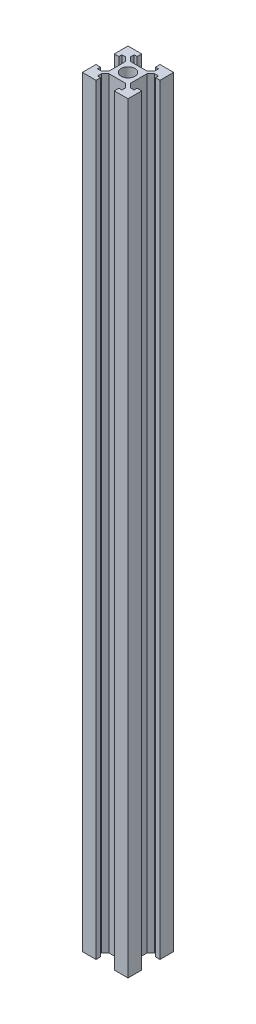
SolidWorks part; units mm, degrees
ref_plane "Front Plane" through (0, 0, 0) normal (0, 0, 1) x (1, 0, 0)
ref_plane "Top Plane" through (0, 0, 0) normal (0, 1, 0) x (1, 0, 0)
ref_plane "Right Plane" through (0, 0, 0) normal (1, 0, 0) x (0, 0, -1)
sketch "Sketch1" plane through (0, 0, 0) normal (0, 1, 0) x (1, 0, 0)
  line L0 (-30, 0) -> (30, 0) construction
  line L3 (-30, 30) -> (-12, 30)
  line L5 (-30, -30) -> (30, 30) construction
  line L6 (-30, 30) -> (30, -30) construction
  line L7 (0, 30) -> (0, -30) construction
  line L8 (-30, 12) -> (-24, 12)
  line L13 (-24, -24) -> (24, 24) construction
  line L14 (-24, 24) -> (24, -24) construction
  line L15 (-14, 24) -> (-14, 16) construction
  line L16 (-24, 16) -> (-19, 16)
  line L17 (-19, 16) -> (-14, 11)
  line L18 (-30, 12) -> (-30, 30)
  line L19 (-14, 11) -> (-14, -11)
  line L20 (-24, 12) -> (-24, 16)
  line L21 (-11, 14) -> (11, 14)
  line L22 (-16, 19) -> (-11, 14)
  line L23 (-12, 24) -> (-16, 24)
  line L24 (-16, 24) -> (-16, 19)
  line L25 (-12, 30) -> (-12, 24)
  line L26 (12, 30) -> (30, 30)
  line L27 (12, 30) -> (12, 24)
  line L28 (12, 24) -> (16, 24)
  line L29 (16, 24) -> (16, 19)
  line L30 (16, 19) -> (11, 14)
  line L31 (14, 11) -> (14, -11)
  line L32 (19, 16) -> (14, 11)
  line L33 (24, 12) -> (24, 16)
  line L34 (24, 16) -> (19, 16)
  line L35 (30, 12) -> (24, 12)
  line L36 (30, 12) -> (30, 30)
  line L37 (-14, -24) -> (-14, -16) construction
  line L38 (30, -12) -> (30, -30)
  line L39 (30, -12) -> (24, -12)
  line L40 (24, -16) -> (19, -16)
  line L41 (24, -12) -> (24, -16)
  line L42 (19, -16) -> (14, -11)
  line L43 (16, -19) -> (11, -14)
  line L44 (16, -24) -> (16, -19)
  line L45 (12, -24) -> (16, -24)
  line L46 (12, -30) -> (12, -24)
  line L47 (12, -30) -> (30, -30)
  line L48 (-12, -30) -> (-12, -24)
  line L49 (-16, -24) -> (-16, -19)
  line L50 (-12, -24) -> (-16, -24)
  line L51 (-16, -19) -> (-11, -14)
  line L52 (-11, -14) -> (11, -14)
  line L53 (-24, -12) -> (-24, -16)
  line L54 (-30, -12) -> (-30, -30)
  line L55 (-19, -16) -> (-14, -11)
  line L56 (-24, -16) -> (-19, -16)
  line L57 (-30, -12) -> (-24, -12)
  line L58 (-30, -30) -> (-12, -30)
  circle A0 centre (0, 0) radius 9
  point P0 (0, 0)
  point P10 (0, 0)
  point P34 (0, 14)
  point P41 (-14, 0)
  point P42 (14, 0)
  point P62 (0, -14)
  dimension "D1" = 18
  dimension "D3" = 12
  dimension "D5" = 16
  dimension "D6" = 5
  dimension "D7" = 5
  dimension "D8" = 6
extrude "Boss-Extrude1" add sketch "Sketch1" along normal blind 1000
